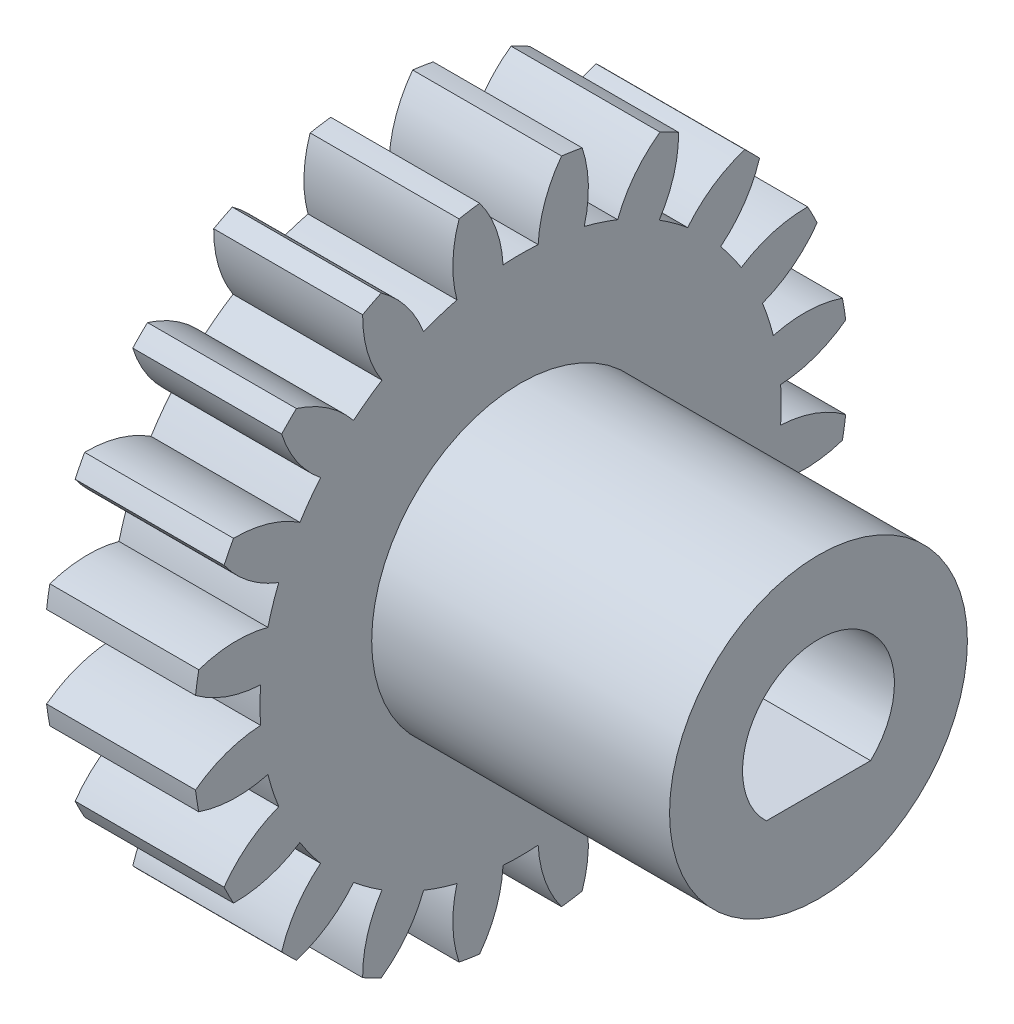
SolidWorks part; units mm, degrees
ref_plane "Plane1" through (0, 0, 0) normal (0, 0, 1) x (1, 0, 0)
ref_plane "Plane2" through (0, 0, 0) normal (0, 1, 0) x (1, 0, 0)
ref_plane "Plane3" through (0, 0, 0) normal (1, 0, 0) x (0, 0, -1)
sketch "HoldingSke" plane through (0, 0, 0) normal (0, 1, 0) x (1, 0, 0)
  line L0 (0, 0) -> (0.9397, -0.342)
  line L1 (-15, 0) -> (100, 0) construction
  line L2 (0, 0) -> (-2.1039, 2.3779)
  line L3 (0, 0) -> (-11.863, 4.5341)
  line L4 (0, 0) -> (8.1152, 2.9537)
  line L5 (0, 0) -> (-46.8476, -17.4728)
  line L6 (0, 0) -> (-4.1448, -2.7965)
  line L7 (-2.1039, 2.3779) -> (8.6586, 51.2059)
  line L8 (-76.2, 54.61) -> (-75.3, 54.61)
  line L9 (-67.7845, 28.3722) -> (-49.3413, 33.142)
  line L10 (-76.2, 71.12) -> (104.1128, 71.12)
  line L11 (0, 0) -> (-5, 0)
  line L12 (-76.2, 101.6) -> (-76.162, 101.6)
  line L13 (24.9733, 27.94) -> (52.9518, 28.4284)
  line L14 (24.9733, 27.94) -> (24.9743, 27.94)
  line L15 (24.9733, 27.94) -> (100.4006, 29.5858)
  line L16 (-63.627, -1) -> (-12.827, -1)
  circle A0 centre (0, 0) radius 2.5
  circle A1 centre (0, 0) radius 8.749
  circle A2 centre (0, 0) radius 37.5
  circle A3 centre (0, 0) radius 2.5
  dimension "MHD" = 17.498
  dimension "Hub_dia" = 75
  dimension "Bore" = 5
  dimension "MBD" = 5
  dimension "Num_teeth" = 20
  dimension "Pitch" = 1
  dimension "Overall_len" = 50
  dimension "Show_teeth" = 20
  dimension "Thickness" = 5
  dimension "OAL" = 50.0001
  dimension "T_dim" = 0.9
  dimension "Ap" = 14.5
  dimension "H" = 19.05
  dimension "Pitch_radius" = 180.3128
  dimension "Width" = 5
  dimension "Backlash" = 0.038
  dimension "Addendum_fac" = 1
  dimension "Dedendum_fac" = 1.25
  dimension "Clearance_fac" = 0.25
  dimension "Dedendum_add" = 0.001
  dimension "Module" = 1
sketch "BasProSke" plane through (0, 0, 0) normal (0, 1, 0) x (1, 0, 0)
  line L0 (-10, 0) -> (60, 0) construction
  line L1 (0, 0) -> (0, 11)
  line L2 (0, 0) -> (5, 0)
  line L3 (5, 0) -> (5, 11)
  line L4 (5, 11) -> (0, 11)
  dimension "Thickness" = 5
  dimension "Diameter" = 22
revolve "Base-Revolve" add sketch "BasProSke" angle 360 about L0
sketch "TooCutSke" plane through (0, 0, 0) normal (1, 0, 0) x (0, 0, -1)
  line L1 (0, 0) -> (0, 107) construction
  line L2 (0, 0) -> (-0.8511, 9.9637) construction
  line L3 (0, 0) -> (-3.1206, 19.7028) construction
  line L4 (-0.8511, 9.9637) -> (-1.5603, 9.8514) construction
  arc A0 (0.5894, 8.7291) -> (-0.5894, 8.7291) centre (0, 0) ccw
  arc A1 (1.3917, 10.9372) -> (-1.3917, 10.9372) centre (0, 0) ccw
  circle A2 centre (0, 0) radius 10 construction
  circle A3 centre (0, 0) radius 9.6815 construction
  arc A4 (-0.5894, 8.7291) -> (-1.3917, 10.9372) centre (-4.5843, 8.5273) ccw
  arc A5 (1.3917, 10.9372) -> (0.5894, 8.7291) centre (4.5843, 8.5273) ccw
  dimension "Root_dia" = 17.498
  dimension "Overcut_dia" = 22.0508
  dimension "Pitch_dia" = 20
  dimension "Base_dia" = 19.363
  dimension "Flank_rad" = 4
  dimension "Half_ang" = 9
  dimension "Half_CT" = 0.7181
extrude "ToothCut" cut sketch "TooCutSke" along normal through all
fillet "Breaks" [suppressed] radius 0.02
fillet "RootFillets" [suppressed] radius 0.251
pattern_circular "TeethCuts" count 20 every 18 about axis through (-10, 0, 0) along (1, 0, 0) of "ToothCut", "RootFillets", "Breaks"
sketch "HubNeaOneSke" plane through (0, 0, 0) normal (-1, 0, 0) x (0, 0, 1)
  circle A0 centre (0, 0) radius 8.749
  dimension "Diameter" = 17.498
extrude "HubNearOne" [suppressed] add sketch "HubNeaOneSke" along normal blind 45.0001
sketch "HubNeaBotSke" plane through (0, 0, 0) normal (-1, 0, 0) x (0, 0, 1)
  circle A0 centre (0, 0) radius 8.749
  dimension "Diameter" = 17.498
extrude "HubNearBoth" [suppressed] add sketch "HubNeaBotSke" along normal blind 22.5
ref_plane "FarPln" through (5, 0, 0) normal (1, 0, 0) x (0, 0, -1)
sketch "HubFarSke" plane through (5, 0, 0) normal (1, 0, 0) x (0, 0, -1)
  circle A0 centre (0, 0) radius 8.749
  dimension "Diameter" = 17.498
extrude "HubFar" [suppressed] add sketch "HubFarSke" along normal blind 22.5
sketch "BorSke" plane through (0, 0, 0) normal (1, 0, 0) x (0, 0, -1)
  circle A0 centre (0, 0) radius 2.5
  dimension "Diameter" = 5
extrude "Bore" cut sketch "BorSke" along normal mid plane 100.0001
sketch "KeySke" plane through (0, 0, 0) normal (1, 0, 0) x (0, 0, -1)
  line L0 (-1, 0) -> (-1, 3.4)
  line L1 (-1, 3.4) -> (1, 3.4)
  line L2 (1, 3.4) -> (1, 0)
  line L3 (0, 0) -> (0, 34) construction
  line L4 (-1, 0) -> (1, 0)
  dimension "Offset" = 3.4
  dimension "Width" = 2
extrude "Keyway" [suppressed] cut sketch "KeySke" along normal mid plane 100.0001
pattern_circular "Keyway2" [suppressed] count 2 every 90 about axis through (-10, 0, 0) along (1, 0, 0)
sketch "Sketch1" plane through (5, 0, 0) normal (1, 0, 0) x (0, 0, -1)
  circle A0 centre (0, 0) radius 5
  dimension "D1" = 10
extrude "Boss-Extrude2" add sketch "Sketch1" along normal blind 10 and the other way through all
sketch "Sketch2" plane through (15, 0, 0) normal (1, 0, 0) x (0, 0, -1)
  line L0 (-1.75, -1.8547) -> (1.75, -1.8547)
  circle A0 centre (0, 0) radius 2.55
  dimension "D1" = 5.1
  dimension "D2" = 3.5
extrude "Cut-Extrude1" cut sketch "Sketch2" against normal through all contours L0 A0
equation "' \"Module@HoldingSke\" = 6.35"
equation "' \"Num_teeth@HoldingSke\" = 12"
equation "' \"Ap@HoldingSke\" =  20"
equation "' \"Ap@HoldingSke\" = 20"
equation "' \"Width@HoldingSke\" = 0.5 * 25.4"
equation "' \"Hub_dia@HoldingSke\"= 1 * 25.4"
equation "' \"Hub_dia@HoldingSke\" = 1 * 25.4"
equation "' \"Overall_len@HoldingSke\" = 1.0 * 25.4"
equation "' \"Bore@HoldingSke\" = 0.75 * 25.4"
equation "' \"T_dim@HoldingSke\" = 0.1 * 25.4"
equation "' \"Width@KeySke\" = 0.25 * 25.4"
equation "' \"Show_teeth@HoldingSke\" = 13"
equation "' \"Backlash@HoldingSke\" = 0.009 * 25.4"
equation "' \"Addendum_fac@HoldingSke\" = 1.0"
equation "' \"Dedendum_fac@HoldingSke\" = 1.25"
equation "' \"Dedendum_add@HoldingSke\" = 0.00005 * 25.4"
equation "' \"Clearance_fac@HoldingSke\" = 0.25"
equation "\"Pitch@HoldingSke\" = 1 / \"Module@HoldingSke\""
equation "\"Overcut_dia@TooCutSke\" = (\"Num_teeth@HoldingSke\" + 2 * \"Addendum_fac@HoldingSke\") / \"Pitch@HoldingSke\" + 0.002 * 25.4"
equation "\"Pitch_dia@TooCutSke\" = \"Num_teeth@HoldingSke\" / \"Pitch@HoldingSke\""
equation "\"Base_dia@TooCutSke\" = \"Num_teeth@HoldingSke\" / \"Pitch@HoldingSke\" * cos((\"Ap@HoldingSke\"  * 3.14159265 / 180))"
equation "\"Root_dia@TooCutSke\" = (\"Num_teeth@HoldingSke\" + 2) / \"Pitch@HoldingSke\" - 2 * (\"Addendum_fac@HoldingSke\" + \"Dedendum_fac@HoldingSke\") / \"Pitch@HoldingSke\" - \"Dedendum_add@HoldingSke\" * 2"
equation "\"Half_ang@TooCutSke\" = 180 / \"Num_teeth@HoldingSke\""
equation "\"Half_CT@TooCutSke\" = \"Num_teeth@HoldingSke\" / \"Pitch@HoldingSke\" * sin((3.14159265 / 2 / \"Num_teeth@HoldingSke\")) / 2 - 7 * \"Backlash@HoldingSke\" / 4"
equation "\"Flank_rad@TooCutSke\" = \"Num_teeth@HoldingSke\" / \"Pitch@HoldingSke\" / 5"
equation "\"Radius@RootFillets\" = \"Clearance_fac@HoldingSke\" / \"Pitch@HoldingSke\" + \"Dedendum_add@HoldingSke\""
equation "\"Break_rad@Breaks\" = 0.02 / \"Pitch@HoldingSke\""
equation "\"Thickness@HoldingSke\" = \"Width@HoldingSke\""
equation "\"OAL@HoldingSke\" = \"Thickness@HoldingSke\""
equation "\"MHD@HoldingSke\" = (\"Num_teeth@HoldingSke\" + 2) / \"Pitch@HoldingSke\" - 2 * (\"Addendum_fac@HoldingSke\" + \"Dedendum_fac@HoldingSke\")  / \"Pitch@HoldingSke\" - \"Dedendum_add@HoldingSke\" * 2"
equation "\"MBD@HoldingSke\" = (\"Num_teeth@HoldingSke\" + 2) / \"Pitch@HoldingSke\" - 2 * (\"Addendum_fac@HoldingSke\" + \"Dedendum_fac@HoldingSke\")  / \"Pitch@HoldingSke\" - \"Dedendum_add@HoldingSke\" * 2 - 0.002 * 25.4"
equation "\"MHD@HoldingSke\" = ((sgn( \"MHD@HoldingSke\" - \"Hub_dia@HoldingSke\" )-1)*( \"MHD@HoldingSke\" - \"Hub_dia@HoldingSke\" ))/-2+ \"Hub_dia@HoldingSke\""
equation "\"MBD@HoldingSke\" = ((sgn( \"MBD@HoldingSke\" - \"Bore@HoldingSke\" )-1)*( \"MBD@HoldingSke\" - \"Bore@HoldingSke\" ))/-2+ \"Bore@HoldingSke\""
equation "\"OAL@HoldingSke\" = ((sgn( \"OAL@HoldingSke\" - \"Overall_len@HoldingSke\" )+1)*( \"OAL@HoldingSke\" - \"Overall_len@HoldingSke\" ))/2 + \"Overall_len@HoldingSke\" + 0.000002 * 25.4"
equation "\"Num_teeth@TeethCuts\" = int( \"Show_teeth@HoldingSke\" ) + 1"
equation "\"Num_teeth@TeethCuts\" = ((sgn( \"Num_teeth@TeethCuts\" - \"Num_teeth@HoldingSke\" )-1)*( \"Num_teeth@TeethCuts\" - \"Num_teeth@HoldingSke\" ))/-2+ \"Num_teeth@HoldingSke\""
equation "\"Num_teeth@TeethCuts\" = ((sgn( \"Num_teeth@TeethCuts\" - 2.0)+1)*( \"Num_teeth@TeethCuts\" - 2.0))/2 +2.0"
equation "\"Angle@TeethCuts\" = 360.0 / \"Num_teeth@HoldingSke\""
equation "\"Diameter@BasProSke\" = (\"Num_teeth@HoldingSke\" + 2 * \"Addendum_fac@HoldingSke\") / \"Pitch@HoldingSke\""
equation "\"Thickness@BasProSke\"  = \"Thickness@HoldingSke\""
equation "' \"Fillet_rad@BasProSke\" =  \"Thickness@HoldingSke\" * 0.05"
equation "' \"Fillet_rad@BasProSke\" = \"Thickness@HoldingSke\" * 0.05"
equation "\"MHD@HoldingSke\" = ((sgn( \"MHD@HoldingSke\" - \"Root_dia@TooCutSke\" )-1)*( \"MHD@HoldingSke\" - \"Root_dia@TooCutSke\" ))/-2+ \"Root_dia@TooCutSke\""
equation "\"Diameter@HubNeaOneSke\" = \"MHD@HoldingSke\""
equation "\"Length@HubNearOne\" = \"OAL@HoldingSke\" - \"Thickness@BasProSke\""
equation "\"Diameter@HubNeaBotSke\" = \"MHD@HoldingSke\""
equation "\"Length@HubNearBoth\" = ( \"OAL@HoldingSke\" - \"Thickness@BasProSke\" ) / 2.0"
equation "\"Thickness@FarPln\" = \"Thickness@BasProSke\""
equation "\"Diameter@HubFarSke\" = \"MHD@HoldingSke\""
equation "\"Length@HubFar\" = ( \"OAL@HoldingSke\" - \"Thickness@BasProSke\" ) / 2.0"
equation "\"Diameter@BorSke\" = \"MBD@HoldingSke\""
equation "\"D1@Bore\" = \"OAL@HoldingSke\" * 2.0"
equation "\"D1@Keyway\" = \"OAL@HoldingSke\" * 2.0"
equation "\"Offset@KeySke\" = \"T_dim@HoldingSke\" + \"MBD@HoldingSke\" / 2.0"
